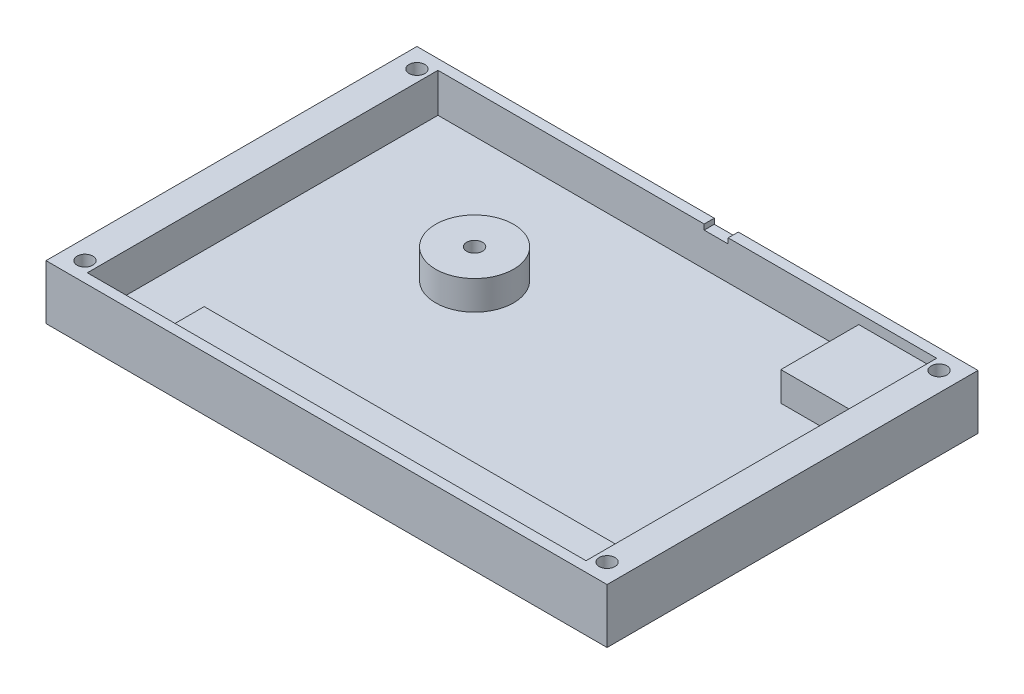
SolidWorks part; units mm, degrees
ref_plane "Front Plane" through (0, 0, 0) normal (0, 0, 1) x (1, 0, 0)
ref_plane "Top Plane" through (0, 0, 0) normal (0, 1, 0) x (1, 0, 0)
ref_plane "Right Plane" through (0, 0, 0) normal (1, 0, 0) x (0, 0, -1)
sketch "Sketch1" plane through (0, 0, 0) normal (0, 1, 0) x (1, 0, 0)
  line L1 (45.72, 30.226) -> (-45.72, 30.226)
  line L2 (45.72, 30.226) -> (45.72, -30.226)
  line L3 (45.72, -30.226) -> (-45.72, -30.226)
  line L4 (-45.72, 30.226) -> (-45.72, -30.226)
  line L5 (45.72, 30.226) -> (-45.72, -30.226) construction
  line L6 (45.72, -30.226) -> (-45.72, 30.226) construction
  point P0 (0, 0)
  dimension "D1" = 60.452
  dimension "D2" = 91.44
extrude "Boss-Extrude1" add sketch "Sketch1" along normal blind 8.89
sketch "Sketch2" plane through (0, 8.89, 0) normal (0, 1, 0) x (1, 0, 0)
  line L1 (40.64, 28.575) -> (-40.64, 28.575)
  line L2 (40.64, 28.575) -> (40.64, -28.575)
  line L3 (40.64, -28.575) -> (-40.64, -28.575)
  line L4 (-40.64, 28.575) -> (-40.64, -28.575)
  line L5 (40.64, 28.575) -> (-40.64, -28.575) construction
  line L6 (40.64, -28.575) -> (-40.64, 28.575) construction
  line L7 (-45.72, -30.226) -> (45.72, -30.226) construction
  point P0 (0, 0)
  dimension "D1" = 57.15
  dimension "D2" = 81.28
  dimension "D3" = 1.651
extrude "Cut-Extrude1" cut sketch "Sketch2" against normal blind 1.6002
sketch "Sketch3" plane through (0, 7.2898, 0) normal (0, 1, 0) x (1, 0, 0)
  line L1 (-40.64, 28.575) -> (27.94, 28.575)
  line L2 (-40.64, 28.575) -> (-40.64, -22.225)
  line L3 (-27.94, -22.225) -> (40.64, -22.225)
  line L4 (27.94, 28.575) -> (27.94, 15.875)
  line L5 (-40.64, -28.575) -> (40.64, -28.575) construction
  line L6 (27.94, 15.875) -> (40.64, 15.875)
  line L7 (-45.72, 30.226) -> (-45.72, -30.226) construction
  line L8 (-27.94, -22.225) -> (-27.94, -28.575)
  line L9 (-40.64, -28.575) -> (40.64, -28.575) construction
  line L10 (-27.94, -28.575) -> (-40.64, -28.575)
  line L11 (-40.64, -28.575) -> (-40.64, -22.225)
  line L12 (40.64, -28.575) -> (40.64, 28.575) construction
  line L13 (40.64, 15.875) -> (40.64, -22.225)
  circle A0 centre (-14.351, 8.255) radius 6.35
  circle A1 centre (-14.351, 8.255) radius 1.2891
  dimension "D3" = 12.7
  dimension "D4" = 2.5781
  dimension "D1" = 12.7
  dimension "D2" = 6.35
  dimension "D5" = 36.83
  dimension "D6" = 31.369
  dimension "D7" = 12.7
  dimension "D8" = 12.7
extrude "Cut-Extrude2" cut sketch "Sketch3" against normal offset from surface (4.7498 mm away) 2.54
sketch "Sketch4" plane through (0, 8.89, 0) normal (0, 1, 0) x (1, 0, 0)
  line L0 (45.72, 30.226) -> (-45.72, 30.226) construction
  line L1 (42.545, 27.051) -> (-42.545, 27.051) construction
  line L2 (42.545, 27.051) -> (42.545, -27.051) construction
  line L3 (42.545, -27.051) -> (-42.545, -27.051) construction
  line L4 (-42.545, 27.051) -> (-42.545, -27.051) construction
  line L5 (42.545, 27.051) -> (-42.545, -27.051) construction
  line L6 (42.545, -27.051) -> (-42.545, 27.051) construction
  line L7 (-45.72, 30.226) -> (-45.72, -30.226) construction
  circle A0 centre (-42.545, 27.051) radius 1.2891
  circle A1 centre (-42.545, -27.051) radius 1.2891
  circle A2 centre (42.545, -27.051) radius 1.2891
  circle A3 centre (42.545, 27.051) radius 1.2891
  point P0 (0, 0)
  dimension "D1" = 2.5781
  dimension "D2" = 3.175
  dimension "D3" = 3.175
extrude "Cut-Extrude3" cut sketch "Sketch4" against normal through all
sketch "Sketch5" plane through (0, 0, -30.226) normal (0, 0, -1) x (-1, 0, 0)
  line L0 (-45.72, 8.89) -> (45.72, 8.89) construction
  line L1 (-2.7432, 8.0264) -> (-6.6548, 8.0264)
  line L2 (-2.7432, 8.0264) -> (-2.7432, 8.89)
  line L3 (-2.7432, 8.89) -> (-6.6548, 8.89)
  line L4 (-6.6548, 8.0264) -> (-6.6548, 8.89)
  line L5 (-2.7432, 8.0264) -> (-6.6548, 8.89) construction
  line L6 (-2.7432, 8.89) -> (-6.6548, 8.0264) construction
  line L7 (45.72, 8.89) -> (45.72, 0) construction
  point P0 (-4.699, 8.4582)
  point P7 (45.72, 4.445)
  dimension "D1" = 50.419
  dimension "D2" = 3.9116
  dimension "D3" = 0.8636
extrude "Cut-Extrude4" cut sketch "Sketch5" against normal up to next
